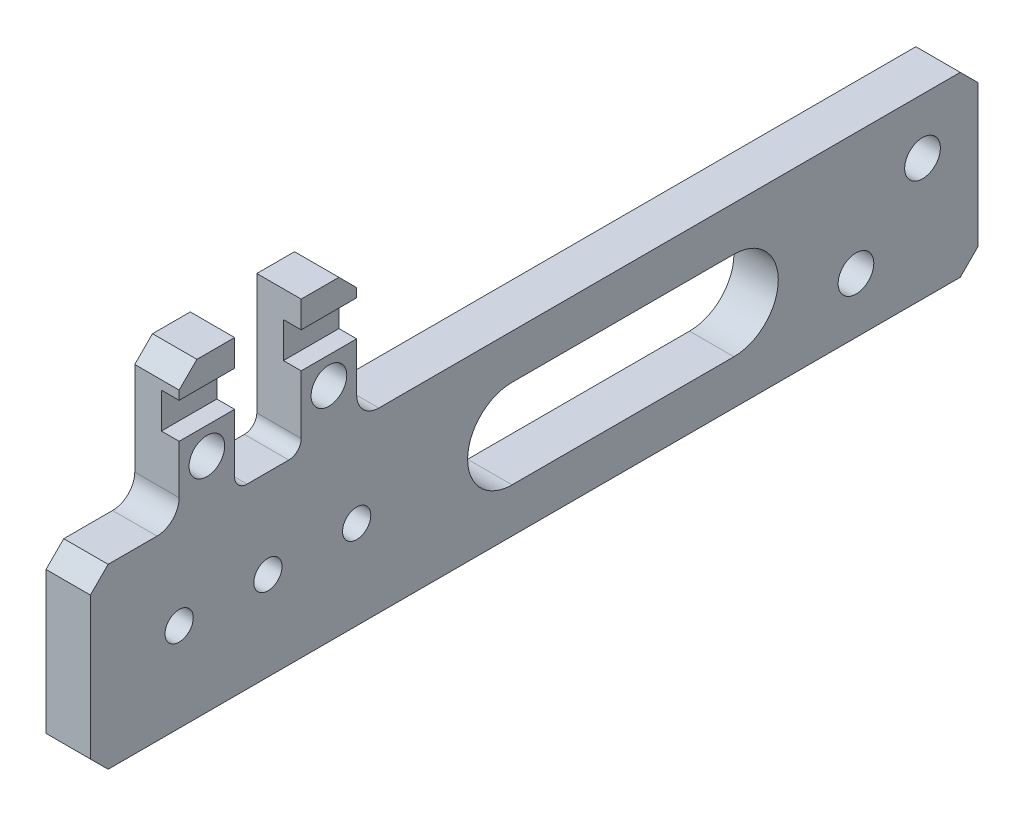
SolidWorks part; units mm, degrees
material "6061-T6 (SS)"
ref_plane "Front" through (0, 0, 0) normal (0, 0, 1) x (1, 0, 0)
ref_plane "Top" through (0, 0, 0) normal (0, 1, 0) x (1, 0, 0)
ref_plane "Right" through (0, 0, 0) normal (1, 0, 0) x (0, 0, -1)
sketch "Sketch1" plane through (0, 0, 0) normal (1, 0, 0) x (0, 0, -1)
  line L1 (0, 0) -> (127, 0)
  line L2 (0, 0) -> (0, 25.4)
  line L3 (0, 25.4) -> (9.525, 25.4)
  line L6 (127, 0) -> (127, 25.4)
  line L7 (38.1, 28.575) -> (38.1, 44.45)
  line L8 (38.1, 44.45) -> (30.1625, 44.45)
  line L9 (12.7, 44.45) -> (12.7, 28.575)
  line L10 (41.275, 25.4) -> (127, 25.4)
  line L11 (50.8, 25.4) -> (38.1, 44.45) construction
  line L12 (12.7, 44.45) -> (0, 25.4) construction
  line L14 (30.1625, 44.45) -> (30.1625, 27.178)
  line L15 (28.3845, 25.4) -> (22.4155, 25.4)
  line L16 (20.6375, 27.178) -> (20.6375, 44.45)
  line L17 (20.6375, 44.45) -> (12.7, 44.45)
  arc A0 (12.7, 28.575) -> (9.525, 25.4) centre (9.525, 28.575) cw
  arc A1 (38.1, 28.575) -> (41.275, 25.4) centre (41.275, 28.575) ccw
  arc A2 (22.4155, 25.4) -> (20.6375, 27.178) centre (22.4155, 27.178) cw
  arc A3 (30.1625, 27.178) -> (28.3845, 25.4) centre (28.3845, 27.178) cw
  point P14 (38.1, 25.4)
  dimension "D3" = 50.8
  dimension "D6" = 3.175
  dimension "D8" = 1.778
  dimension "D1" = 25.4
  dimension "D2" = 19.05
  dimension "D4" = 127
  dimension "D5" = 25.4
  dimension "D7" = 9.525
extrude "Boss-Extrude1" add sketch "Sketch1" along normal blind 6.35
hole_wizard "#10-32 Tapped Hole1" positions "Sketch2" profile "Sketch3" tap size "#10-32" standard "ANSI Inch" end condition through all
sketch "Sketch2" plane through (6.35, 0, 0) normal (1, 0, 0) x (0, 0, -1)
  line L0 (0, 0) -> (12.7, 12.7) construction
  line L1 (12.7, 12.7) -> (25.4, 12.7) construction
  line L2 (25.4, 12.7) -> (38.1, 12.7) construction
  line L3 (38.1, 12.7) -> (50.8, 25.4) construction
  line L4 (9.525, 25.4) -> (0, 25.4) construction
  line L6 (0, 25.4) -> (0, 0) construction
  point P0 (12.7, 12.7)
  point P2 (25.4, 12.7)
  point P4 (38.1, 12.7)
  dimension "D1" = 50.8
  dimension "D2" = 12.7
sketch "Sketch3" plane through (6.35, 12.7, -12.7) normal (0, 1, 0) x (0, 0, -1)
  line L0 (0, 0) -> (0, 6.35)
  line L1 (0, 6.35) -> (2.0193, 6.35)
  line L2 (2.0193, 6.35) -> (2.0193, 0)
  line L5 (2.0193, 0) -> (0, 0)
  line L11 (0, -6.35) -> (0, 107.95) construction
  dimension "Thru Tap Drill Dia." = 4.0386
  dimension "Thru Tap Drill Depth" = 6.35
cosmetic thread "Hole Thread1" parameters "D2"=4.826
cosmetic thread "Hole Thread2" parameters "D2"=4.826
cosmetic thread "Hole Thread3" parameters "D2"=4.826
hole_wizard "#10 Clearance Hole1" positions "Sketch4" profile "Sketch5" hole size "#10" standard "ANSI Inch" end condition through all
sketch "Sketch4" plane through (6.35, 0, 0) normal (1, 0, 0) x (0, 0, -1)
  line L0 (101.6, 0) -> (109.5375, 7.9375) construction
  line L1 (0, 0) -> (127, 0) construction
  line L2 (109.5375, 7.9375) -> (119.0625, 17.4625) construction
  line L3 (119.0625, 17.4625) -> (127, 25.4) construction
  line L5 (127, 0) -> (127, 25.4) construction
  line L6 (20.6375, 44.45) -> (16.6688, 31.75) construction
  line L7 (16.6688, 31.75) -> (12.7, 44.45) construction
  line L10 (30.1625, 44.45) -> (34.1313, 31.75) construction
  line L11 (34.1313, 31.75) -> (38.1, 44.45) construction
  line L13 (9.525, 25.4) -> (0, 25.4) construction
  point P13 (119.0625, 17.4625)
  point P15 (109.5375, 7.9375)
  point P37 (34.1313, 31.75)
  point P39 (16.6688, 31.75)
  dimension "D1" = 25.4
  dimension "D2" = 9.525
  dimension "D3" = 6.35
sketch "Sketch5" plane through (6.35, 17.4625, -119.0625) normal (0, 1, 0) x (0, 0, -1)
  line L0 (0, 0) -> (0, 6.35)
  line L1 (0, 6.35) -> (2.5527, 6.35)
  line L2 (2.5527, 6.35) -> (2.5527, 0)
  line L5 (2.5527, 0) -> (0, 0)
  line L11 (0, -6.35) -> (0, 107.95) construction
  dimension "Thru Hole Dia." = 5.1054
  dimension "Thru Hole Depth" = 6.35
sketch "Sketch6" plane through (6.35, 0, 0) normal (1, 0, 0) x (0, 0, -1)
  line L0 (12.7, 44.45) -> (12.7, 28.575) construction
  line L1 (12.7, 40.64) -> (38.1, 40.64)
  line L2 (12.7, 40.64) -> (12.7, 35.56)
  line L3 (12.7, 35.56) -> (38.1, 35.56)
  line L4 (38.1, 40.64) -> (38.1, 35.56)
  line L5 (38.1, 28.575) -> (38.1, 44.45) construction
  line L6 (9.525, 25.4) -> (0, 25.4) construction
  point P8 (12.7, 38.1)
  dimension "D1" = 5.08
  dimension "D2" = 12.7
extrude "Cut-Extrude1" cut sketch "Sketch6" against normal blind 2.54
chamfer "Chamfer1" distance 2.54 angle 45 6 edges at (3.175, 44.45, -38.1) (3.175, 44.45, -12.7) (3.175, 25.4, -127) (3.175, 0, -127) (3.175, 0, 0) (3.175, 25.4, 0)
sketch "Sketch7" plane through (6.35, 0, 0) normal (1, 0, 0) x (0, 0, -1)
  line L0 (60.325, 12.7) -> (92.075, 12.7) construction
  line L1 (60.325, 19.05) -> (92.075, 19.05)
  line L2 (60.325, 6.35) -> (92.075, 6.35)
  line L3 (0, 22.86) -> (0, 2.54) construction
  line L4 (127, 2.54) -> (127, 22.86) construction
  line L5 (2.54, 0) -> (124.46, 0) construction
  arc A0 (60.325, 19.05) -> (60.325, 6.35) centre (60.325, 12.7) ccw
  arc A1 (92.075, 6.35) -> (92.075, 19.05) centre (92.075, 12.7) ccw
  point P2 (76.2, 12.7)
  dimension "D1" = 12.7
  dimension "D2" = 53.975
  dimension "D3" = 28.575
  dimension "D4" = 12.7
extrude "Cut-Extrude2" cut sketch "Sketch7" against normal through all
